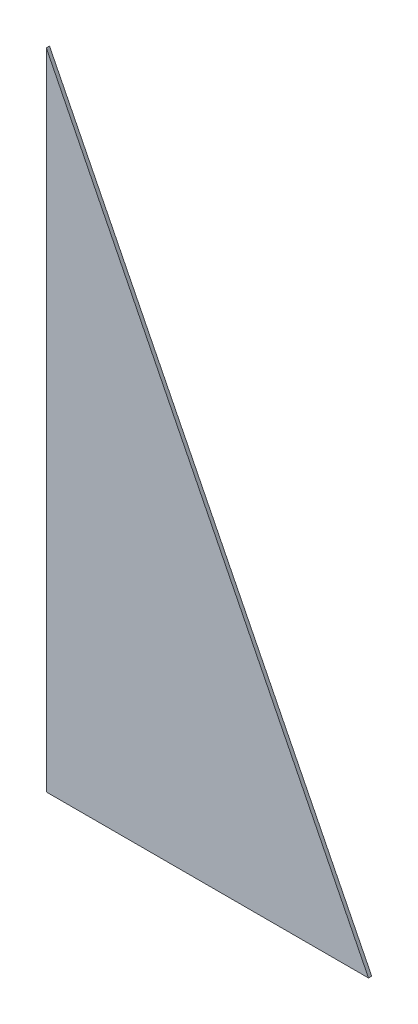
SolidWorks part; units mm, degrees
material "1060 Alloy"
ref_plane "Front Plane" through (0, 0, 0) normal (0, 0, 1) x (1, 0, 0)
ref_plane "Top Plane" through (0, 0, 0) normal (0, 1, 0) x (1, 0, 0)
ref_plane "Right Plane" through (0, 0, 0) normal (1, 0, 0) x (0, 0, -1)
sketch "Sketch2" plane through (0, 0, 0) normal (0, 0, 1) x (1, 0, 0)
  line L0 (0, 0) -> (1000, 0)
  line L1 (1000, 0) -> (0, 2000)
  line L2 (0, 2000) -> (0, 0)
  point P4 (0, 0)
  point P5 (0, 0)
  point P6 (0, 0)
  point P7 (0, 0)
  point P8 (0, 0)
  point P9 (0, 0)
  dimension "D1" = 1000
  dimension "D2" = 2000
extrude "Boss-Extrude2" add sketch "Sketch2" along normal mid plane 10
